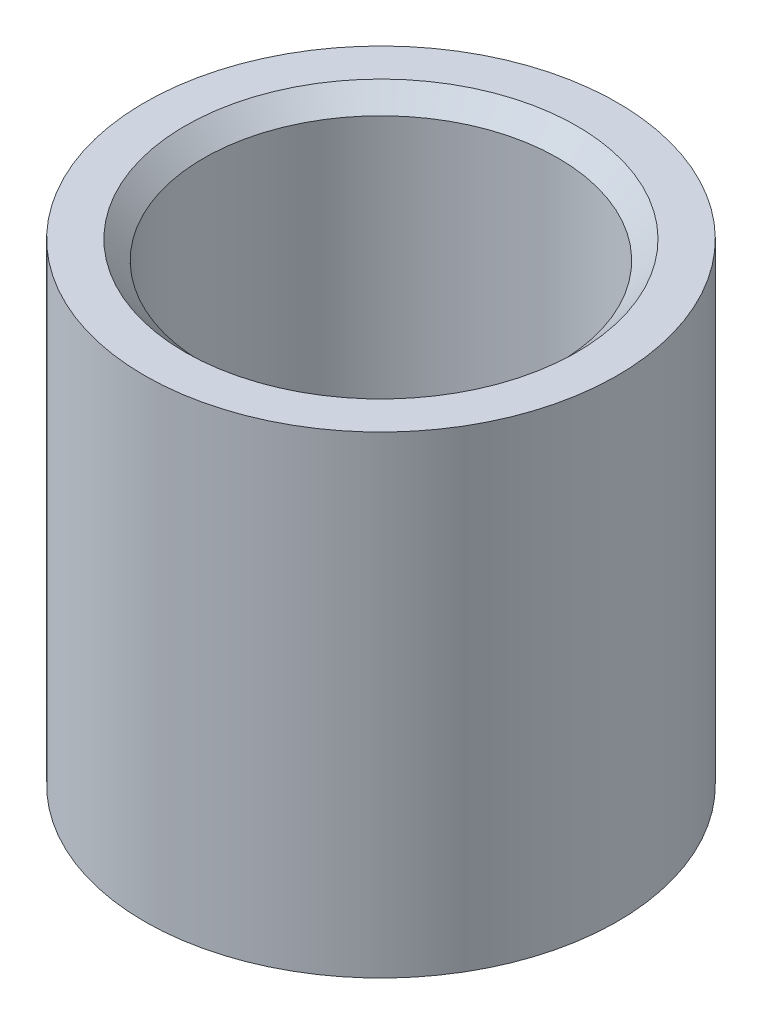
SolidWorks part; units mm, degrees
material "Brass"
ref_plane "Front Plane" through (0, 0, 0) normal (0, 0, 1) x (1, 0, 0)
ref_plane "Top Plane" through (0, 0, 0) normal (0, 1, 0) x (1, 0, 0)
ref_plane "Right Plane" through (0, 0, 0) normal (1, 0, 0) x (0, 0, -1)
sketch "Sketch1" plane through (0, 0, 0) normal (0, 1, 0) x (1, 0, 0)
  circle A0 centre (0, 0) radius 2.3813
  circle A1 centre (0, 0) radius 3.175
  dimension "D1" = 4.7625
  dimension "D2" = 6.35
extrude "Boss-Extrude1" add sketch "Sketch1" along normal blind 6.35
chamfer "Chamfer1" distance 0.25 angle 45 2 edges at (0, 0, 2.3813) (0, 6.35, 2.3813)
